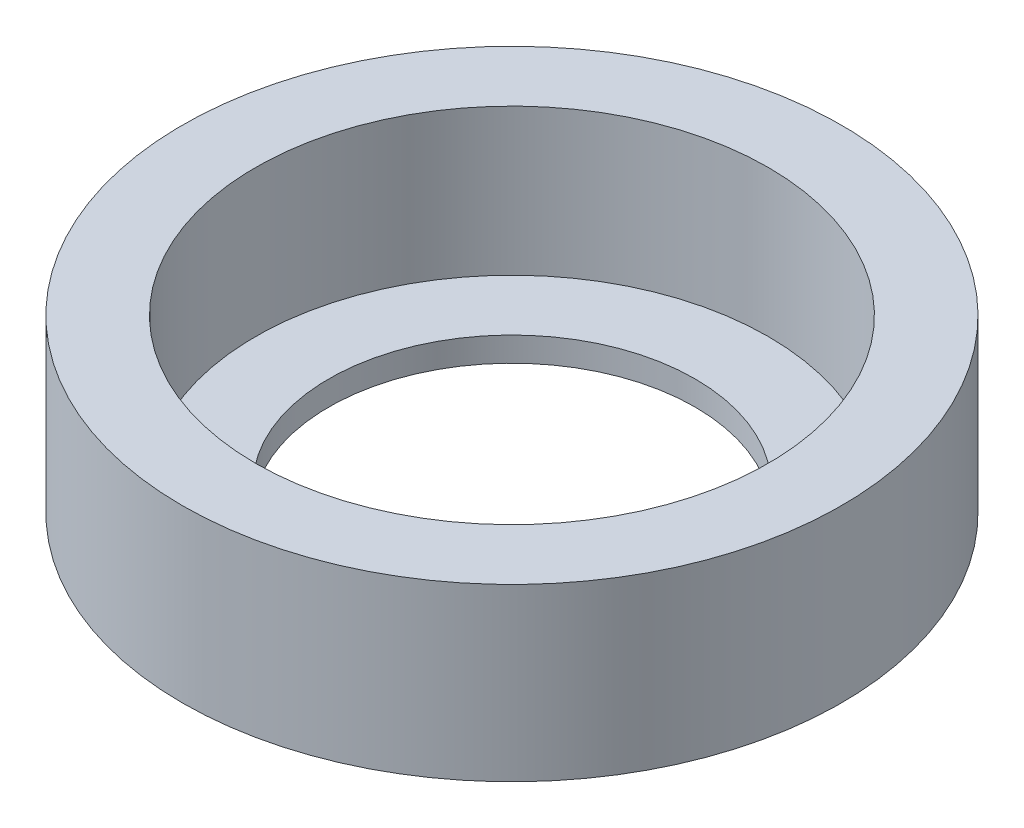
SolidWorks part; units mm, degrees
ref_plane "Piano frontale" through (0, 0, 0) normal (0, 0, 1) x (1, 0, 0)
ref_plane "Piano superiore" through (0, 0, 0) normal (0, 1, 0) x (1, 0, 0)
ref_plane "Piano destro" through (0, 0, 0) normal (1, 0, 0) x (0, 0, -1)
sketch "Schizzo1" plane through (0, 0, 0) normal (0, 1, 0) x (1, 0, 0)
  circle A0 centre (0, 0) radius 7.5
  circle A1 centre (0, 0) radius 13.5
  dimension "D1" = 15
  dimension "D2" = 27
extrude "Estrusione-Estrusione1" add sketch "Schizzo1" along normal blind 7
sketch "Schizzo2" plane through (0, 7, 0) normal (0, 1, 0) x (1, 0, 0)
  circle A0 centre (0, 0) radius 10.5
extrude "Taglio-Estrusione1" cut sketch "Schizzo2" against normal blind 6
